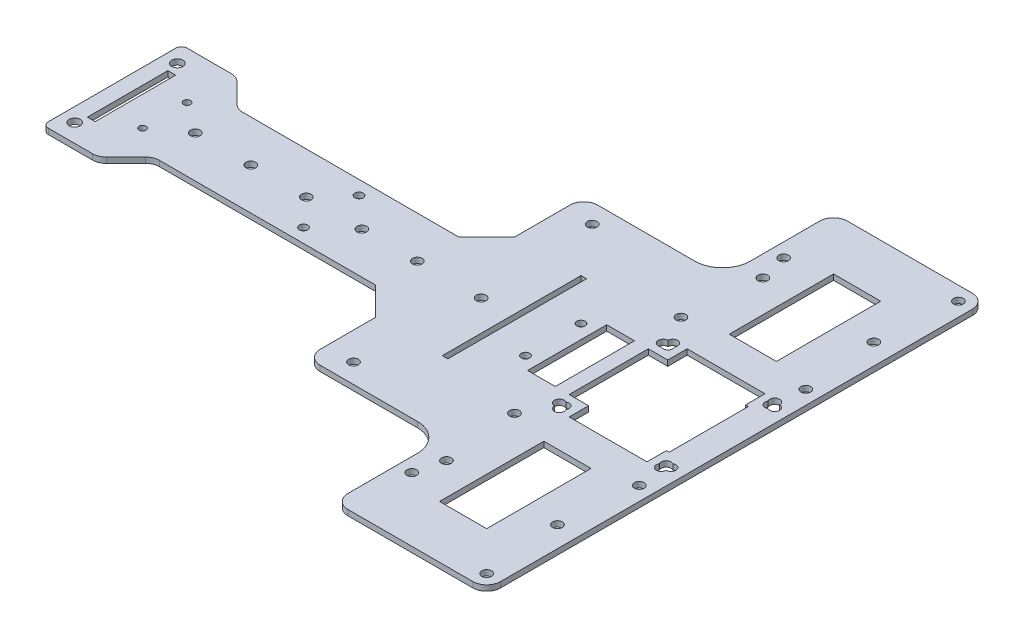
SolidWorks part; units mm, degrees
material "Acrylic (Medium-high impact)"
ref_plane "Front Plane" through (0, 0, 0) normal (0, 0, 1) x (1, 0, 0)
ref_plane "Top Plane" through (0, 0, 0) normal (0, 1, 0) x (1, 0, 0)
ref_plane "Right Plane" through (0, 0, 0) normal (1, 0, 0) x (0, 0, -1)
sketch "Sketch1" plane through (0, 0, 0) normal (0, 1, 0) x (1, 0, 0)
  line L0 (0, 0) -> (72.5, 0) construction
  line L1 (-125, 125) -> (125, 125) construction
  line L2 (-125, 125) -> (-125, -125) construction
  line L3 (-125, -125) -> (125, -125) construction
  line L4 (125, 125) -> (125, -125) construction
  line L5 (-125, 125) -> (125, -125) construction
  line L6 (-125, -125) -> (125, 125) construction
  line L7 (75, -85) -> (75, -67) construction
  line L8 (20, 90) -> (125, 90)
  line L9 (20, 90) -> (20, 25)
  line L10 (20, -90) -> (125, -90)
  line L11 (125, 90) -> (125, -90)
  line L12 (20, 90) -> (125, -90) construction
  line L13 (20, -90) -> (125, 90) construction
  line L14 (125, -90) -> (125, -85) construction
  line L19 (-137.5, 0) -> (137.5, 0) construction
  line L20 (20, 25) -> (-100, 25)
  line L21 (125, -85) -> (120, -85) construction
  line L22 (120, -85) -> (75, -85) construction
  line L23 (120, -85) -> (120, -30) construction
  line L24 (120, -30) -> (75, -30) construction
  line L25 (20, -25) -> (-100, -25)
  line L26 (20, -25) -> (20, -90)
  line L27 (-100, 25) -> (-100, -25)
  line L28 (-100, 0) -> (-95, 0) construction
  line L29 (-95, 0) -> (-95, -18.5) construction
  line L30 (-95, 0) -> (-93, 0) construction
  line L31 (-93, 0) -> (-81, 0) construction
  line L32 (-94.4, 14.5) -> (-91.6, 14.5)
  line L33 (-94.4, 14.5) -> (-94.4, -14.5)
  line L34 (-94.4, -14.5) -> (-91.6, -14.5)
  line L35 (-91.6, 14.5) -> (-91.6, -14.5)
  line L36 (-94.4, 14.5) -> (-91.6, -14.5) construction
  line L37 (-94.4, -14.5) -> (-91.6, 14.5) construction
  line L38 (-81, 0) -> (-81, 8) construction
  line L39 (75, -67) -> (75, -43) construction
  line L40 (75, -43) -> (30, -43) construction
  circle A5 centre (120, -85) radius 1.75
  circle A7 centre (120, 85) radius 1.75
  circle A9 centre (75, -67) radius 1.75
  circle A13 centre (120, -30) radius 1.75
  circle A15 centre (75, -30) radius 1.75
  circle A17 centre (75, 67) radius 1.75
  circle A18 centre (-95, -18.5) radius 2
  circle A19 centre (-95, 18.5) radius 2
  circle A20 centre (-81, 8) radius 1.25
  circle A21 centre (-81, -8) radius 1.25
  circle A22 centre (120, 30) radius 1.75
  circle A23 centre (75, 30) radius 1.75
  circle A24 centre (30, -43) radius 1.75
  circle A25 centre (30, 43) radius 1.75
  point P0 (0, 0)
  point P28 (100, 0)
  dimension "D8" = 65
  dimension "D9" = 65
  dimension "D12" = 3.5
  dimension "D14" = 5
  dimension "D16" = 18.5
  dimension "D17" = 4
  dimension "D18" = 3.5
  dimension "D20" = 3.5
  dimension "D6" = 3.5
  dimension "D26" = 2.5
  dimension "D29" = 3.5
  dimension "D1" = 250
  dimension "D2" = 72.5
  dimension "D3" = 180
  dimension "D4" = 105
  dimension "D5" = 18
  dimension "D7" = 120
  dimension "D10" = 5
  dimension "D11" = 5
  dimension "D13" = 45
  dimension "D15" = 55
  dimension "D19" = 45
  dimension "D21" = 2
  dimension "D22" = 29
  dimension "D23" = 2.8
  dimension "D24" = 12
  dimension "D25" = 8
  dimension "D27" = 24
  dimension "D28" = 45
extrude "Boss-Extrude1" add sketch "Sketch1" along normal blind 2
sketch "Sketch3" plane through (0, 2, 0) normal (0, 1, 0) x (1, 0, 0)
  line L0 (125, 90) -> (125, 71) construction
  line L1 (125, -90) -> (125, 90) construction
  line L2 (125, 71) -> (106, 71) construction
  line L3 (125, 0) -> (100, 0) construction
  line L4 (106, 71) -> (89, 71)
  line L5 (106, 71) -> (106, 33.4)
  line L6 (106, 33.4) -> (89, 33.4)
  line L7 (89, 71) -> (89, 33.4)
  line L12 (97.5, 71) -> (97.5, 57) construction
  line L13 (97.5, 57) -> (77.5, 57) construction
  line L14 (-1.1, 0) -> (1.1, 0) construction
  line L15 (106, -71) -> (89, -71)
  line L16 (89, -71) -> (89, -33.4)
  line L17 (106, -33.4) -> (89, -33.4)
  line L18 (106, -71) -> (106, -33.4)
  line L19 (100, 0) -> (114.0195, 14.2637) construction
  line L20 (118.37, 18.69) -> (81.63, 18.69) construction
  line L21 (118.37, 18.69) -> (118.37, -18.69) construction
  line L26 (118.37, -18.69) -> (81.63, -18.69) construction
  line L29 (81.63, 18.69) -> (81.63, -18.69) construction
  line L52 (118.37, 18.69) -> (81.63, -18.69) construction
  line L53 (118.37, -18.69) -> (81.63, 18.69) construction
  line L54 (100, 0) -> (85.9805, 14.2637) construction
  line L55 (100, 0) -> (85.9805, -14.2637) construction
  line L56 (85.9805, 14.2637) -> (85.9805, 21.2637)
  line L57 (85.9805, 21.2637) -> (114.0195, 21.2637)
  line L58 (114.0195, 21.2637) -> (114.0195, 14.2637)
  line L59 (114.0195, 14.2637) -> (115.0195, 14.2637)
  line L60 (115.0195, 14.2637) -> (115.0195, -14.2637)
  line L61 (115.0195, -14.2637) -> (114.0195, -14.2637)
  line L62 (114.0195, -14.2637) -> (114.0195, -21.2637)
  line L63 (114.0195, -21.2637) -> (85.9805, -21.2637)
  line L64 (85.9805, -21.2637) -> (85.9805, -14.2637)
  line L65 (85.9805, -14.2637) -> (78.9805, -14.2637)
  line L66 (78.9805, -14.2637) -> (78.9805, 14.2637)
  line L67 (78.9805, 14.2637) -> (85.9805, 14.2637)
  line L68 (100, 0) -> (45, 0) construction
  line L69 (45, 0) -> (33, 0) construction
  line L70 (44, 25) -> (46, 25)
  line L71 (44, 25) -> (44, -25)
  line L72 (44, -25) -> (46, -25)
  line L73 (46, 25) -> (46, -25)
  line L74 (44, 25) -> (46, -25) construction
  line L75 (44, -25) -> (46, 25) construction
  line L76 (78.9805, 14.2637) -> (73.9805, 14.2637) construction
  line L77 (20, -90) -> (70, -90)
  line L78 (20, -90) -> (20, -50)
  line L79 (20, -50) -> (70, -50)
  line L80 (70, -90) -> (70, -50)
  line L81 (20, 90) -> (70, 90)
  line L82 (20, 90) -> (20, 50)
  line L83 (20, 50) -> (70, 50)
  line L84 (70, 90) -> (70, 50)
  line L86 (73.9805, 14.2637) -> (63.9805, 14.2637)
  line L87 (73.9805, 14.2637) -> (73.9805, -14.2637)
  line L88 (73.9805, -14.2637) -> (63.9805, -14.2637)
  line L89 (63.9805, 14.2637) -> (63.9805, -14.2637)
  circle A0 centre (77.5, 57) radius 1.75
  circle A1 centre (117.5, 57) radius 1.75
  circle A2 centre (117.5, -57) radius 1.75
  circle A3 centre (77.5, -57) radius 1.75
  circle A19 centre (81.63, 18.69) radius 1.75
  circle A20 centre (118.37, 18.69) radius 1.75
  circle A21 centre (81.63, -18.69) radius 1.75
  circle A22 centre (118.37, -18.69) radius 1.75
  circle A23 centre (33, 0) radius 1.75
  dimension "D7" = 3.5
  dimension "D10" = 36.74
  dimension "D12" = 3.5
  dimension "D11" = 3.5
  dimension "D13" = 3.5
  dimension "D14" = 3.5
  dimension "D26" = 3.5
  dimension "D1" = 19
  dimension "D2" = 19
  dimension "D3" = 37.6
  dimension "D4" = 17
  dimension "D5" = 14
  dimension "D6" = 20
  dimension "D8" = 25
  dimension "D9" = 37.38
  dimension "D15" = 20
  dimension "D16" = 20
  dimension "D17" = 20
  dimension "D18" = 7
  dimension "D19" = 1
  dimension "D20" = 7
  dimension "D21" = 7
  dimension "D22" = 55
  dimension "D23" = 50
  dimension "D24" = 2
  dimension "D25" = 12
  dimension "D27" = 40
  dimension "D28" = 50
  dimension "D29" = 40
  dimension "D30" = 50
  dimension "D31" = 5
  dimension "D32" = 10
extrude "Cut-Extrude1" cut sketch "Sketch3" against normal blind 10
fillet "Fillet1" radius 2 2 edges at (-100, 1, -25) (-100, 1, 25)
fillet "Fillet2" radius 5 6 edges at (20, 1, -50) (70, 1, -90) (125, 1, -90) (125, 1, 90) (70, 1, 90) (20, 1, 50)
fillet "Fillet3" radius 10 2 edges at (70, 1, 50) (70, 1, -50)
sketch "Sketch4" plane through (0, 2, 0) normal (0, 1, 0) x (1, 0, 0)
  arc A0 (118.37, 18.69) -> (120.12, 20.44) centre (120.12, 18.69) ccw
  circle A1 centre (118.37, 18.69) radius 1.75 construction
  arc A2 (120.12, 20.44) -> (118.37, 18.69) centre (118.37, 20.44) ccw
  arc A3 (120.12, -20.44) -> (118.37, -18.69) centre (120.12, -18.69) ccw
  circle A4 centre (118.37, -18.69) radius 1.75 construction
  arc A5 (118.37, -18.69) -> (120.12, -20.44) centre (118.37, -20.44) ccw
  arc A6 (79.88, -20.44) -> (81.63, -18.69) centre (81.63, -20.44) ccw
  circle A7 centre (81.63, -18.69) radius 1.75 construction
  arc A8 (81.63, -18.69) -> (79.88, -20.44) centre (79.88, -18.69) ccw
  arc A9 (79.88, 20.44) -> (81.63, 18.69) centre (79.88, 18.69) ccw
  circle A10 centre (81.63, 18.69) radius 1.75 construction
  arc A11 (81.63, 18.69) -> (79.88, 20.44) centre (81.63, 20.44) ccw
extrude "Cut-Extrude2" cut sketch "Sketch4" against normal blind 10
sketch "Sketch5" plane through (0, 2, 0) normal (0, 1, 0) x (1, 0, 0)
  line L0 (20, 25) -> (-80, 25)
  line L1 (20, 25) -> (-98, 25) construction
  line L2 (-80, 25) -> (-80, 15) construction
  line L3 (-80, 15) -> (-70, 15) construction
  line L4 (-70, 15) -> (-80, 25)
  line L5 (20, 25) -> (20, 15) construction
  line L6 (20, 15) -> (10, 15) construction
  line L7 (-70, 15) -> (10, 15)
  line L8 (10, 15) -> (20, 25)
  line L9 (-1.1, 0) -> (1.1, 0) construction
  line L10 (-70, -15) -> (10, -15)
  line L11 (10, -15) -> (20, -25)
  line L12 (-70, -15) -> (-80, -25)
  line L13 (20, -25) -> (-80, -25)
  line L14 (-70, 15) -> (-70, 0) construction
  line L15 (63.9805, 0) -> (58.9805, 0) construction
  line L16 (63.9805, 14.2637) -> (63.9805, -14.2637) construction
  line L17 (58.9805, 0) -> (58.9805, 10) construction
  circle A0 centre (-70, 0) radius 1.75
  circle A1 centre (-50, 0) radius 1.75
  circle A2 centre (-30, 0) radius 1.75
  circle A3 centre (-10, 0) radius 1.75
  circle A4 centre (10, 0) radius 1.75
  circle A5 centre (58.9805, 10) radius 1.5
  circle A6 centre (58.9805, -10) radius 1.5
  circle A7 centre (-21.0195, 10) radius 1.5
  circle A8 centre (-21.0195, -10) radius 1.5
  dimension "D6" = 3.5
  dimension "D10" = 3
  dimension "D1" = 100
  dimension "D2" = 10
  dimension "D3" = 10
  dimension "D4" = 10
  dimension "D5" = 10
  dimension "D8" = 5
  dimension "D9" = 10
  dimension "D7" = 5
  dimension "D11" = 2
extrude "Cut-Extrude3" cut sketch "Sketch5" against normal blind 10
fillet "Fillet4" radius 5 4 edges at (-80, 1, -25) (-70, 1, -15) (-70, 1, 15) (-80, 1, 25)
